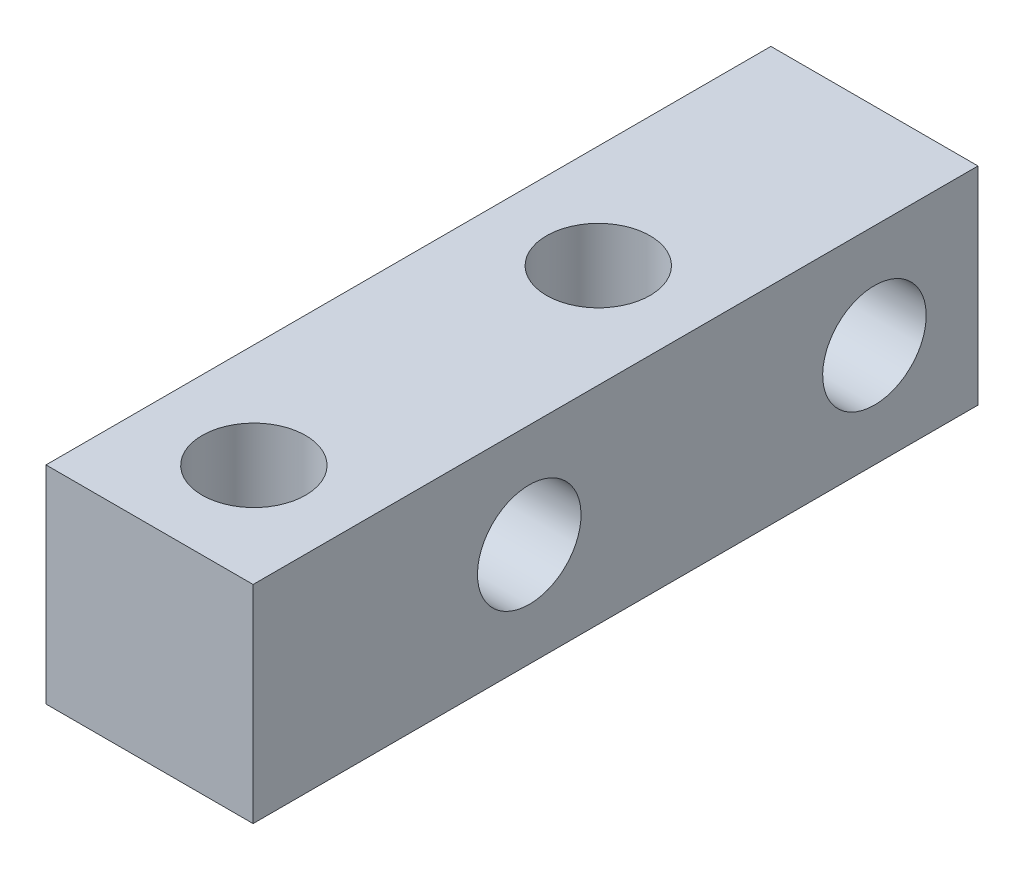
SolidWorks part; units mm, degrees
material "延性铁 (SN)"
ref_plane "前视基准面" through (0, 0, 0) normal (0, 0, 1) x (1, 0, 0)
ref_plane "上视基准面" through (0, 0, 0) normal (0, 1, 0) x (1, 0, 0)
ref_plane "右视基准面" through (0, 0, 0) normal (1, 0, 0) x (0, 0, -1)
sketch "草图1" plane through (0, 0, 0) normal (0, 0, 1) x (1, 0, 0)
  line L1 (-3, 3) -> (3, 3)
  line L2 (-3, 3) -> (-3, -3)
  line L3 (-3, -3) -> (3, -3)
  line L4 (3, 3) -> (3, -3)
  line L5 (-3, 3) -> (3, -3) construction
  line L6 (-3, -3) -> (3, 3) construction
  point P0 (0, 0)
  dimension "D1" = 6
  dimension "D2" = 6
extrude "凸台-拉伸1" add sketch "草图1" along normal blind 21
sketch "草图2" plane through (-3, 0, 0) normal (-1, 0, 0) x (0, 0, 1)
  line L0 (0, 3) -> (0, -3) construction
  circle A0 centre (3, 0) radius 1.5
  circle A1 centre (13, 0) radius 1.5
  dimension "D1" = 3
  dimension "D2" = 10
extrude "切除-拉伸1" cut sketch "草图2" against normal blind 21
sketch "草图3" plane through (0, 3, 0) normal (0, 1, 0) x (1, 0, 0)
  line L0 (3, -21) -> (-3, -21) construction
  circle A0 centre (0.0215, -18) radius 1.5
  circle A1 centre (0, -8) radius 1.5
  dimension "D1" = 3
  dimension "D2" = 10
extrude "切除-拉伸2" cut sketch "草图3" against normal blind 21
